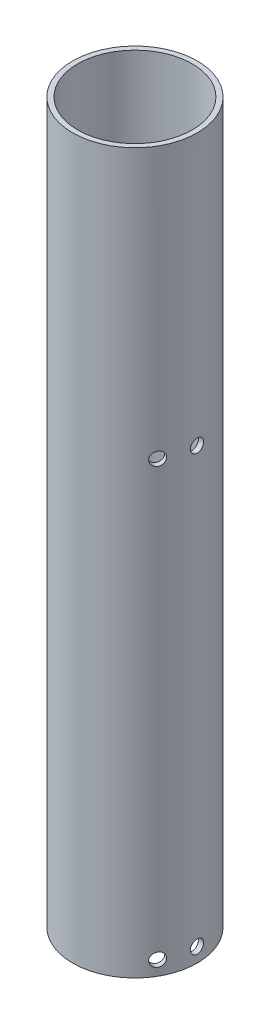
SolidWorks part; units mm, degrees
ref_plane "Front Plane" through (0, 0, 0) normal (0, 0, 1) x (1, 0, 0)
ref_plane "Top Plane" through (0, 0, 0) normal (0, 1, 0) x (1, 0, 0)
ref_plane "Right Plane" through (0, 0, 0) normal (1, 0, 0) x (0, 0, -1)
sketch "Sketch1" plane through (0, 0, 0) normal (0, 1, 0) x (1, 0, 0)
  circle A0 centre (0, 0) radius 26
  circle A1 centre (0, 0) radius 23.9
  dimension "D1" = 52
  dimension "D2" = 47.8
extrude "Boss-Extrude1" add sketch "Sketch1" along normal blind 300
sketch "Sketch3" plane through (0, 0, 0) normal (0, 0, 1) x (1, 0, 0)
  line L0 (0, 6) -> (0, 0)
  line L1 (0, 6) -> (0, 187)
  circle A0 centre (0, 6) radius 2.75
  circle A1 centre (0, 187) radius 2.75
  dimension "D2" = 5.5
  dimension "D3" = 5.5
  dimension "D1" = 6
  dimension "D4" = 181
extrude "Cut-Extrude2" cut sketch "Sketch3" against normal through all
pattern_circular "CirPattern1" count 3 over 360 about axis through (0, 300, 0) along (0, -1, 0) of "Cut-Extrude2"
sketch "Sketch5" plane through (0, 0, 0) normal (1, 0, 0) x (0, 0, -1)
  line L0 (0, 6) -> (0, 0)
  line L1 (0, 6) -> (0, 187)
  circle A0 centre (0, 187) radius 2.75
  circle A1 centre (0, 6) radius 2.75
  point P4 (0, 0)
  point P8 (0.2709, 187)
  dimension "D2" = 5.5
  dimension "D1" = 6
  dimension "D4" = 5.5
  dimension "D3" = 181
extrude "Cut-Extrude3" cut sketch "Sketch5" against normal through all both and the other way through all
equation "\"TubeOutsideDiameter\"= 52"
equation "\"D1@Sketch1\"=\"TubeOutsideDiameter\""
equation "\"TubeInnerDiameter\"= 47.8"
equation "\"ReleaseMechanisumHeight\"=100"
equation "\"WireDiameter\"=3.38983"
equation "\"servoHoleDiameter\" = 2.8"
equation "\"CordDiameter\"= 5"
equation "\"MountingBoldDiameter\"=2.8"
equation "\"TubeMountingBoltDiameter\" = 5"
equation "\"D2@Sketch1\"=\"TubeInnerDiameter\""
equation "\"CardTubeOutsideDiameter\"= 54.2"
equation "\"CardTubeInsideDiameter\"= 50.4"
equation "\"D1@Sketch3\"=6"
equation "\"D2@Sketch3\"=\"TubeMountingBoltDiameter\"+0.5"
equation "\"D3@Sketch3\"=\"TubeMountingBoltDiameter\"+0.5"
equation "\"D2@Sketch5\"=\"TubeMountingBoltDiameter\"+0.5"
equation "\"D4@Sketch5\"=\"TubeMountingBoltDiameter\"+0.5"
